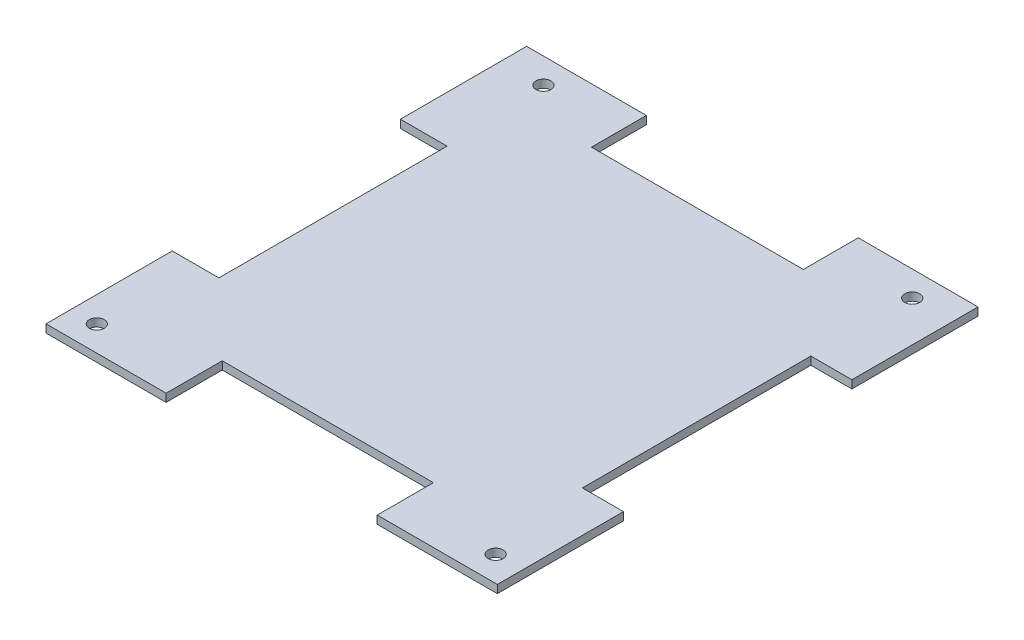
SolidWorks part; units mm, degrees
material "Custom Plastic"
ref_plane "Front Plane" through (0, 0, 0) normal (0, 0, 1) x (1, 0, 0)
ref_plane "Top Plane" through (0, 0, 0) normal (0, 1, 0) x (1, 0, 0)
ref_plane "Right Plane" through (0, 0, 0) normal (1, 0, 0) x (0, 0, -1)
sketch "Sketch2" plane through (0, 0, 0) normal (0, 1, 0) x (1, 0, 0)
  line L1 (0, 0) -> (84.57, 0)
  line L2 (0, 0) -> (0, 90.8)
  line L3 (0, 90.8) -> (84.57, 90.8)
  line L4 (84.57, 0) -> (84.57, 90.8)
extrude "Boss-Extrude1" add sketch "Sketch2" along normal blind 1.6
sketch "Sketch3" plane through (0, 1.6, 0) normal (0, 1, 0) x (1, 0, 0)
  line L3 (0, 0) -> (84.57, 0) construction
  line L4 (84.57, 90.8) -> (0, 90.8) construction
  circle A0 centre (2.5, 2.5) radius 1.5
  circle A1 centre (82.07, 2.5) radius 1.5
  circle A2 centre (5.8, 88.3) radius 1.5
  circle A3 centre (79.37, 88.3) radius 1.5
extrude "Cut-Extrude1" cut sketch "Sketch3" against normal through all
sketch "Sketch4" plane through (84.57, 0, 0) normal (1, 0, 0) x (0, 0, -1)
  line L1 (90.8, 1.6) -> (0, 1.6)
  line L2 (90.8, 1.6) -> (90.8, 0)
  line L3 (90.8, 0) -> (0, 0)
  line L4 (0, 1.6) -> (0, 0)
extrude "Boss-Extrude2" add sketch "Sketch4" along normal blind 2.88
sketch "Sketch5" plane through (0, 0, 0) normal (-1, 0, 0) x (0, 0, 1)
  line L1 (-90.8, 0) -> (0, 0)
  line L2 (-90.8, 0) -> (-90.8, 1.6)
  line L3 (-90.8, 1.6) -> (0, 1.6)
  line L4 (0, 0) -> (0, 1.6)
extrude "Boss-Extrude3" add sketch "Sketch5" along normal blind 2.59
sketch "Sketch6" plane through (0, 0, -90.8) normal (0, 0, -1) x (-1, 0, 0)
  line L1 (2.59, 0) -> (-87.45, 0)
  line L2 (2.59, 0) -> (2.59, 1.6)
  line L3 (2.59, 1.6) -> (-87.45, 1.6)
  line L4 (-87.45, 0) -> (-87.45, 1.6)
extrude "Boss-Extrude4" add sketch "Sketch6" along normal blind 2.54
sketch "Sketch7" plane through (0, 0, 0) normal (0, 0, 1) x (1, 0, 0)
  line L1 (87.45, 1.6) -> (-2.59, 1.6)
  line L2 (87.45, 1.6) -> (87.45, 0)
  line L3 (87.45, 0) -> (-2.59, 0)
  line L4 (-2.59, 1.6) -> (-2.59, 0)
extrude "Boss-Extrude5" add sketch "Sketch7" along normal blind 2.54
sketch "Sketch8" plane through (0, 1.6, 0) normal (0, 1, 0) x (1, 0, 0)
  line L0 (87.45, 93.34) -> (87.45, -2.54) construction
  line L1 (95.6363, 68.1858) -> (79.2637, 68.1858)
  line L2 (95.6363, 68.1858) -> (95.6363, 22.6142)
  line L3 (95.6363, 22.6142) -> (79.2637, 22.6142)
  line L4 (79.2637, 68.1858) -> (79.2637, 22.6142)
  line L5 (95.6363, 68.1858) -> (79.2637, 22.6142) construction
  line L6 (95.6363, 22.6142) -> (79.2637, 68.1858) construction
  line L7 (-2.59, 93.34) -> (87.45, 93.34) construction
  line L8 (63.5632, 104.2905) -> (21.2968, 104.2905)
  line L9 (63.5632, 104.2905) -> (63.5632, 82.3895)
  line L10 (63.5632, 82.3895) -> (21.2968, 82.3895)
  line L11 (21.2968, 104.2905) -> (21.2968, 82.3895)
  line L12 (63.5632, 104.2905) -> (21.2968, 82.3895) construction
  line L13 (63.5632, 82.3895) -> (21.2968, 104.2905) construction
  line L14 (-2.59, -2.54) -> (-2.59, 93.34) construction
  line L15 (6.7185, 68.1601) -> (-11.8985, 68.1601)
  line L16 (6.7185, 68.1601) -> (6.7185, 22.6399)
  line L17 (6.7185, 22.6399) -> (-11.8985, 22.6399)
  line L18 (-11.8985, 68.1601) -> (-11.8985, 22.6399)
  line L19 (6.7185, 68.1601) -> (-11.8985, 22.6399) construction
  line L20 (6.7185, 22.6399) -> (-11.8985, 68.1601) construction
  line L21 (87.45, -2.54) -> (-2.59, -2.54) construction
  line L22 (63.4894, 8.6601) -> (21.3706, 8.6601)
  line L23 (63.4894, 8.6601) -> (63.4894, -13.7401)
  line L24 (63.4894, -13.7401) -> (21.3706, -13.7401)
  line L25 (21.3706, 8.6601) -> (21.3706, -13.7401)
  line L26 (63.4894, 8.6601) -> (21.3706, -13.7401) construction
  line L27 (63.4894, -13.7401) -> (21.3706, 8.6601) construction
  point P0 (87.45, 45.4)
  point P7 (42.43, 93.34)
  point P14 (-2.59, 45.4)
  point P21 (42.43, -2.54)
extrude "Cut-Extrude2" cut sketch "Sketch8" against normal through all
